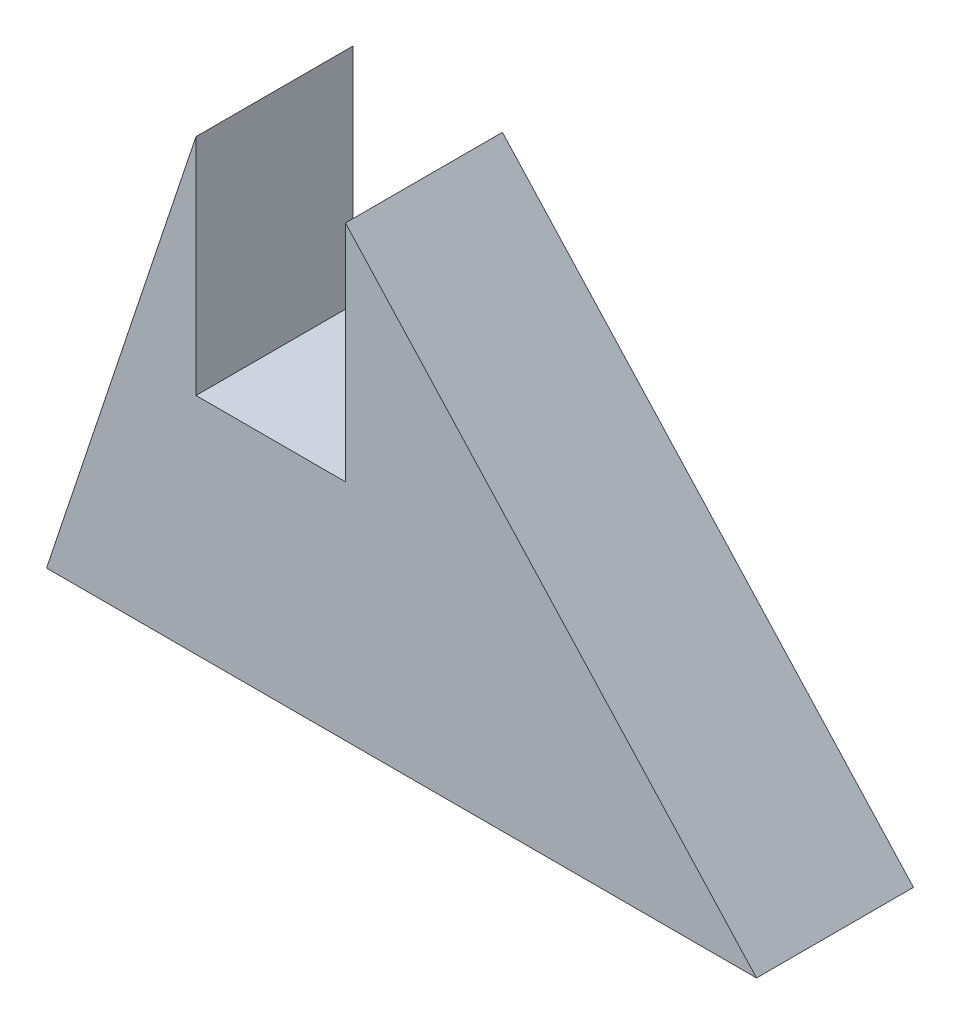
SolidWorks part; units mm, degrees
ref_plane "Front Plane" through (0, 0, 0) normal (0, 0, 1) x (1, 0, 0)
ref_plane "Top Plane" through (0, 0, 0) normal (0, 1, 0) x (1, 0, 0)
ref_plane "Right Plane" through (0, 0, 0) normal (1, 0, 0) x (0, 0, -1)
sketch "Sketch1" plane through (0, 0, 0) normal (0, 0, 1) x (1, 0, 0)
  line L0 (0, 0) -> (20, 60)
  line L1 (20, 60) -> (40, 60)
  line L2 (40, 60) -> (95, 0)
  line L4 (40, 60) -> (40, 0) construction
  line L5 (20, 60) -> (20, 0) construction
  line L6 (0, 0) -> (20, 0)
  line L7 (20, 0) -> (40, 0)
  line L8 (40, 0) -> (95, 0)
  dimension "D1" = 60
  dimension "D2" = 20
  dimension "D3" = 20
  dimension "D4" = 55
extrude "Boss-Extrude1" add sketch "Sketch1" along normal blind 21
sketch "Sketch2" plane through (0, 0, 21) normal (0, 0, 1) x (1, 0, 0)
  line L0 (20, 60) -> (20, 30)
  line L1 (20, 60) -> (40, 60)
  line L2 (40, 60) -> (40, 30)
  line L3 (40, 30) -> (20, 30)
  line L4 (20, 30) -> (20, 0) construction
  line L5 (0, 0) -> (95, 0) construction
extrude "Cut-Extrude1" cut sketch "Sketch2" against normal up to surface (21 mm away) up to face at (38.75, 30, 0)
